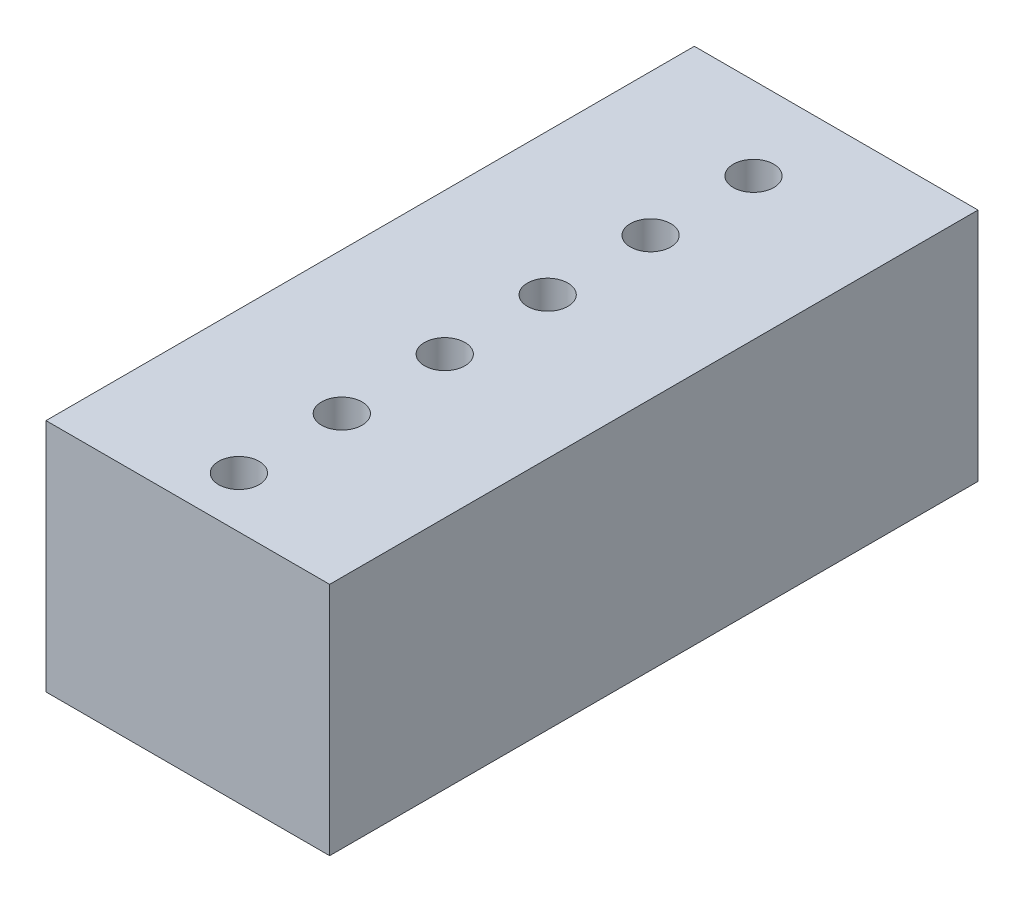
SolidWorks part; units mm, degrees
ref_plane "Front Plane" through (0, 0, 0) normal (0, 0, 1) x (1, 0, 0)
ref_plane "Top Plane" through (0, 0, 0) normal (0, 1, 0) x (1, 0, 0)
ref_plane "Right Plane" through (0, 0, 0) normal (1, 0, 0) x (0, 0, -1)
sketch "Sketch1" plane through (0, 0, 0) normal (0, 1, 0) x (1, 0, 0)
  line L1 (3.5, 8) -> (-3.5, 8)
  line L2 (3.5, 8) -> (3.5, -8)
  line L3 (3.5, -8) -> (-3.5, -8)
  line L4 (-3.5, 8) -> (-3.5, -8)
  line L5 (3.5, 8) -> (-3.5, -8) construction
  line L6 (3.5, -8) -> (-3.5, 8) construction
  line L7 (-0.96, 13.19) -> (1.58, 13.19) construction
  circle A0 centre (0, 13.19) radius 0.5
  circle A1 centre (1.58, 13.19) radius 0.5 construction
  point P0 (0, 0)
  point P13 (0, 8)
  dimension "D1" = 7
  dimension "D2" = 16
extrude "Boss-Extrude1" add sketch "Sketch1" along normal mid plane 5.8
sketch "Sketch2" plane through (0, 2.9, 0) normal (0, 1, 0) x (1, 0, 0)
  line L0 (3.5, 8) -> (-3.5, 8) construction
  circle A0 centre (0, 5.96) radius 0.5
  dimension "D1" = 1
  dimension "D2" = 2.04
extrude "Cut-Extrude1" cut sketch "Sketch2" against normal through all
pattern_linear "LPattern1" count 12 spacing 2.54 along (0, 0, 1) of "Cut-Extrude1"
